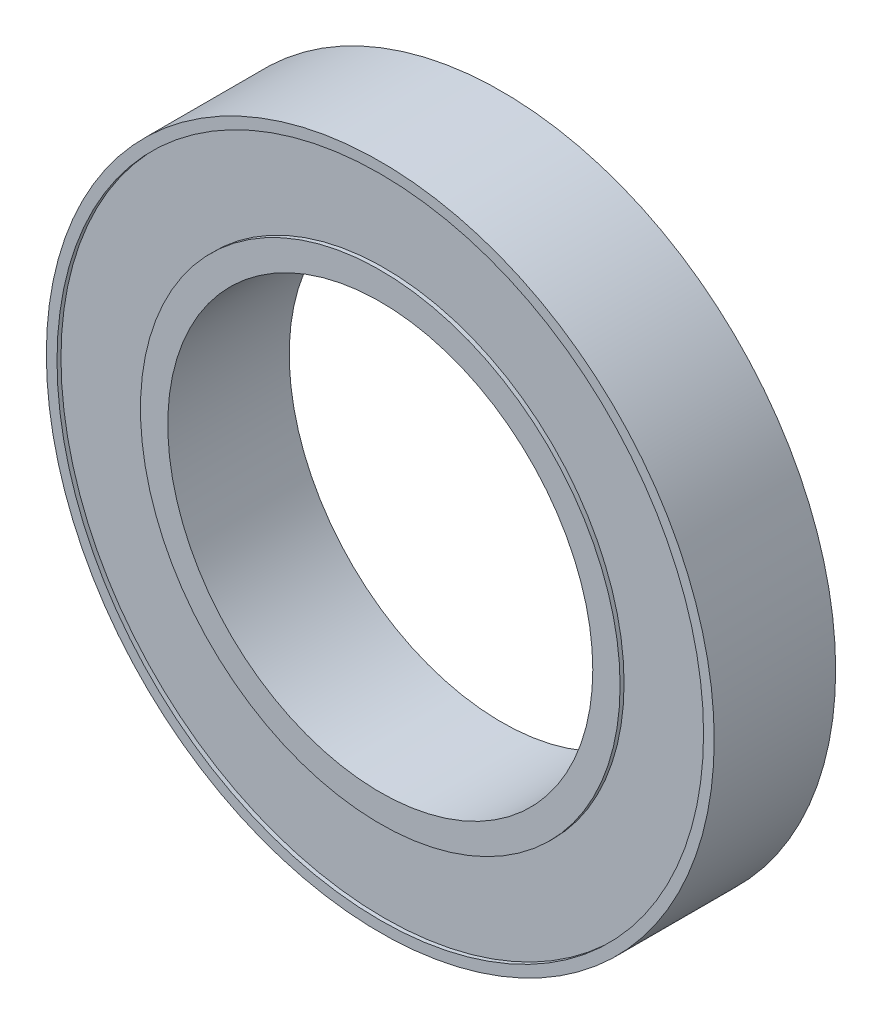
SolidWorks part; units mm, degrees
ref_plane "Front Plane" through (0, 0, 0) normal (0, 0, 1) x (1, 0, 0)
ref_plane "Top Plane" through (0, 0, 0) normal (0, 1, 0) x (1, 0, 0)
ref_plane "Right Plane" through (0, 0, 0) normal (1, 0, 0) x (0, 0, -1)
sketch "Sketch1" plane through (0, 0, 0) normal (0, 1, 0) x (1, 0, 0)
  line L0 (0, 0) -> (0, 35.6121) construction
  line L1 (17.5, -5) -> (17.5, 5)
  line L2 (17.5, 5) -> (19.7491, 5)
  line L3 (19.7491, 5) -> (19.7491, 4.673)
  line L4 (19.7491, 4.673) -> (26.621, 4.673)
  line L5 (26.621, 4.673) -> (26.621, 5)
  line L6 (26.621, 5) -> (27.5, 5)
  line L7 (27.5, 5) -> (27.5, -5)
  line L8 (0, 0) -> (42.7751, 0) construction
  line L9 (26.621, -5) -> (27.5, -5)
  line L10 (26.621, -4.673) -> (26.621, -5)
  line L11 (19.7491, -4.673) -> (26.621, -4.673)
  line L12 (19.7491, -5) -> (19.7491, -4.673)
  line L13 (17.5, -5) -> (19.7491, -5)
  point P13 (27.5, 0)
  point P18 (17.5, 0)
  dimension "D1" = 35
  dimension "D2" = 55
  dimension "D3" = 10
revolve "Revolve1" add sketch "Sketch1" angle 360 about L0
